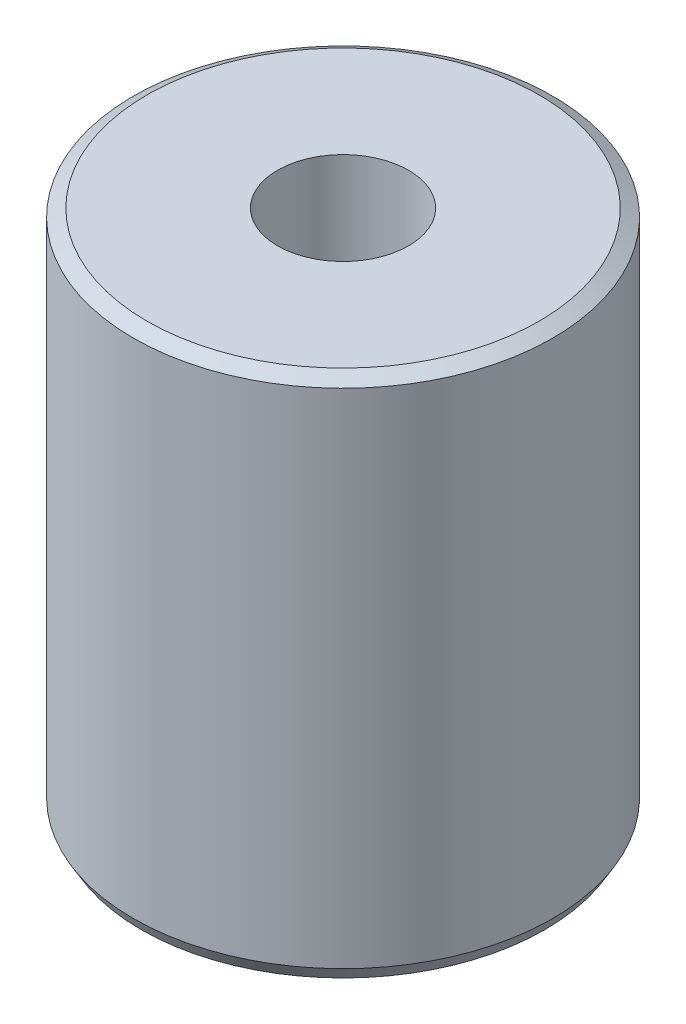
SolidWorks part; units mm, degrees
ref_plane "Front Plane" through (0, 0, 0) normal (0, 0, 1) x (1, 0, 0)
ref_plane "Top Plane" through (0, 0, 0) normal (0, 1, 0) x (1, 0, 0)
ref_plane "Right Plane" through (0, 0, 0) normal (1, 0, 0) x (0, 0, -1)
sketch "Sketch1" plane through (0, 0, 0) normal (0, 1, 0) x (1, 0, 0)
  circle A0 centre (0, 0) radius 4
  dimension "D1" = 8
extrude "Boss-Extrude1" add sketch "Sketch1" along normal blind 10
chamfer "Chamfer1" distance 0.15 angle 60 2 edges at (0, 0, 4) (0, 10, 4)
hole_wizard "M3x0.5 Tapped Hole1" positions "Sketch2" profile "Sketch3" tap size "M3x0.5" standard "ANSI Metric" end condition through all
sketch "Sketch2" plane through (0, 10, 0) normal (0, 1, 0) x (1, 0, 0)
  point P0 (0, 0)
cosmetic thread "Hole Thread3"
sketch "Sketch3" plane through (0, 10, 0) normal (1, 0, 0) x (0, 0, 1)
  line L0 (0, 0) -> (0, 10)
  line L1 (0, 10) -> (1.25, 10)
  line L2 (1.25, 10) -> (1.25, 0)
  line L5 (1.25, 0) -> (0, 0)
  line L11 (0, -6.35) -> (0, 107.95) construction
  dimension "Thru Tap Drill Dia." = 2.5
  dimension "Thru Tap Drill Depth" = 10
